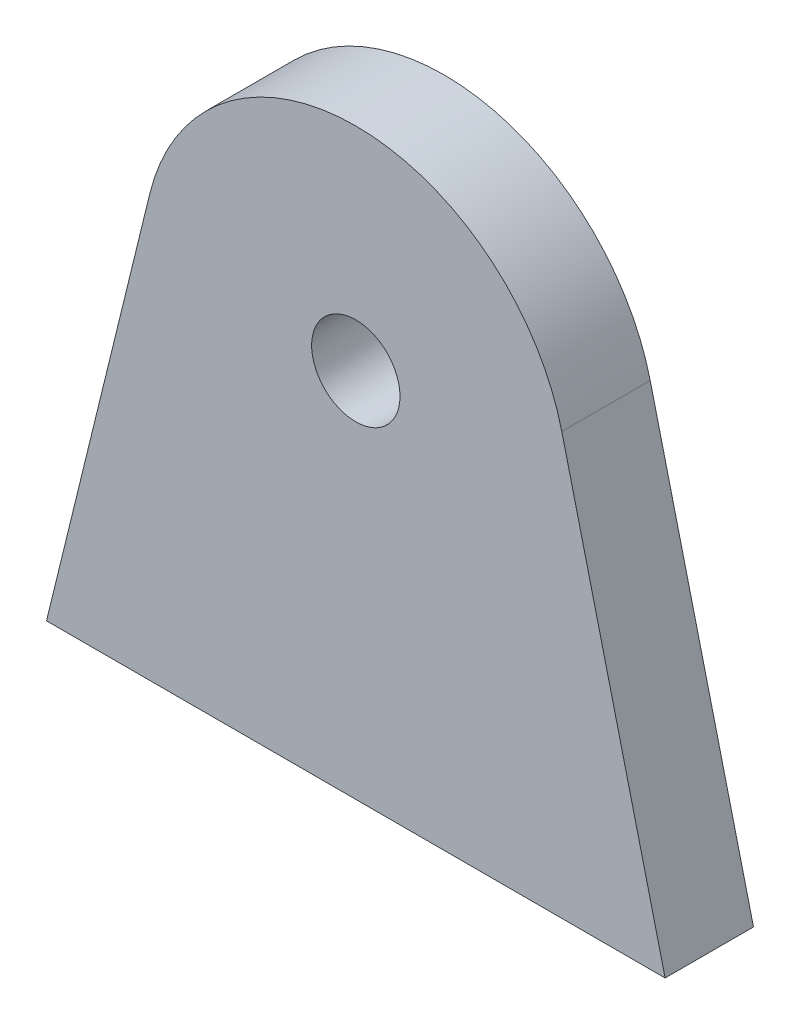
SolidWorks part; units mm, degrees
ref_plane "Płaszczyzna przednia" through (0, 0, 0) normal (0, 0, 1) x (1, 0, 0)
ref_plane "Płaszczyzna górna" through (0, 0, 0) normal (0, 1, 0) x (1, 0, 0)
ref_plane "Płaszczyzna prawa" through (0, 0, 0) normal (1, 0, 0) x (0, 0, -1)
sketch "Szkic1" plane through (0, 0, 0) normal (0, 0, 1) x (1, 0, 0)
  line L0 (0, 0) -> (0, 30.3175) construction
  line L1 (17.5, 0) -> (-17.5, 0)
  line L2 (-17.5, 0) -> (-11.6553, 23.8556)
  line L3 (17.5, 0) -> (11.6553, 23.8556)
  circle A0 centre (0, 21) radius 2.5
  arc A1 (-11.6553, 23.8556) -> (11.6553, 23.8556) centre (0, 21) cw
  point P4 (0, 0)
  point P15 (0, 71.4274)
  dimension "D3" = 12
  dimension "D4" = 5
  dimension "D1" = 21
  dimension "D2" = 35
extrude "Dodanie-wyciągnięcie1" add sketch "Szkic1" along normal blind 5
